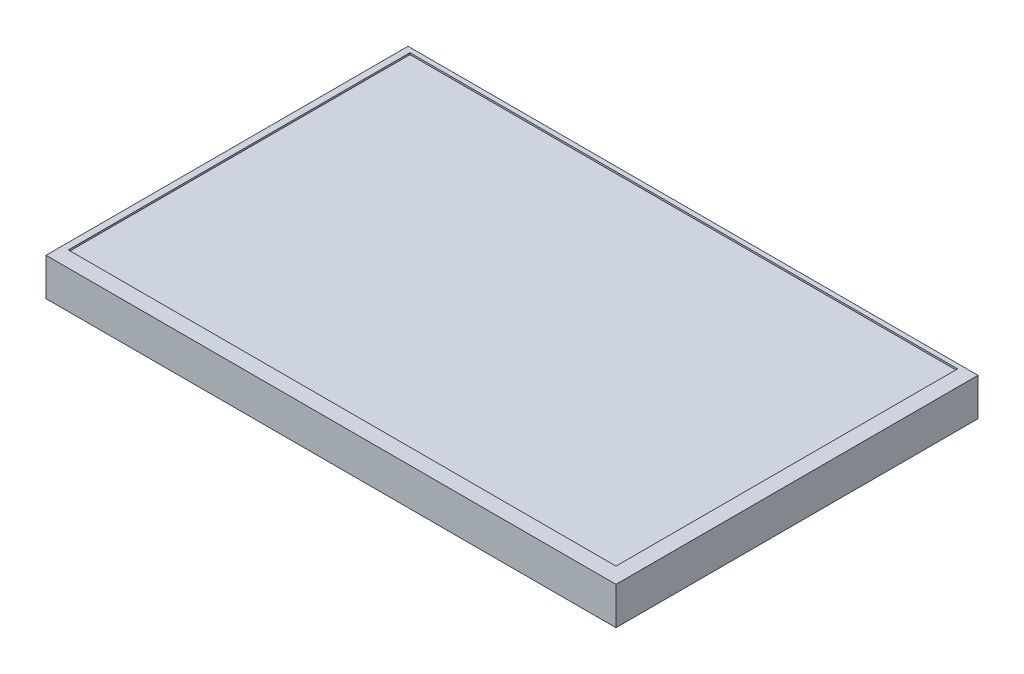
SolidWorks part; units mm, degrees
ref_plane "Front Plane" through (0, 0, 0) normal (0, 0, 1) x (1, 0, 0)
ref_plane "Top Plane" through (0, 0, 0) normal (0, 1, 0) x (1, 0, 0)
ref_plane "Right Plane" through (0, 0, 0) normal (1, 0, 0) x (0, 0, -1)
sketch "Sketch1" plane through (0, 0, 0) normal (0, 1, 0) x (1, 0, 0)
  line L1 (-83, 52.72) -> (83, 52.72)
  line L2 (-83, 52.72) -> (-83, -52.72)
  line L3 (-83, -52.72) -> (83, -52.72)
  line L4 (83, 52.72) -> (83, -52.72)
  line L5 (-83, 52.72) -> (83, -52.72) construction
  line L6 (-83, -52.72) -> (83, 52.72) construction
  point P0 (0, 0)
  dimension "D1" = 166
  dimension "D2" = 105.44
extrude "Boss-Extrude1" add sketch "Sketch1" along normal blind 10.95
sketch "Sketch2" plane through (0, 10.95, 0) normal (0, 1, 0) x (1, 0, 0)
  line L0 (-83, 52.72) -> (-83, -52.72) construction
  line L1 (-81.1, 51.37) -> (78.4, 51.37)
  line L2 (-81.1, 51.37) -> (-81.1, -48.12)
  line L3 (-81.1, -48.12) -> (78.4, -48.12)
  line L4 (78.4, 51.37) -> (78.4, -48.12)
  line L5 (83, 52.72) -> (-83, 52.72) construction
  line L6 (-83, -52.72) -> (83, -52.72) construction
  line L7 (83, -52.72) -> (83, 52.72) construction
  dimension "D1" = 1.9
  dimension "D2" = 1.35
  dimension "D3" = 4.6
  dimension "D4" = 4.6
extrude "Cut-Extrude1" cut sketch "Sketch2" against normal blind 0.5
